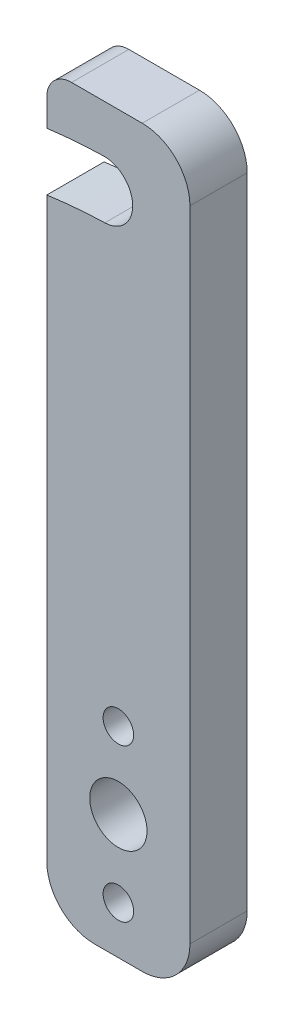
SolidWorks part; units mm, degrees
material "MDF"
ref_plane "Plano frontal" through (0, 0, 0) normal (0, 0, 1) x (1, 0, 0)
ref_plane "Plano superior" through (0, 0, 0) normal (0, 1, 0) x (1, 0, 0)
ref_plane "Plano direito" through (0, 0, 0) normal (1, 0, 0) x (0, 0, -1)
sketch "Esboço1" plane through (0, 0, 0) normal (0, 0, 1) x (1, 0, 0)
  line L0 (0, -17.4894) -> (0, -33.4894) construction
  line L1 (-7.5, -38.4894) -> (7.5, -38.4894)
  line L2 (-7.5, -38.4894) -> (-7.5, 38.4894)
  line L3 (-7.5, 38.4894) -> (7.5, 38.4894)
  line L4 (7.5, -38.4894) -> (7.5, 38.4894)
  line L5 (-7.5, -38.4894) -> (7.5, 38.4894) construction
  line L6 (-7.5, 38.4894) -> (7.5, -38.4894) construction
  circle A0 centre (0, -33.4894) radius 1.6
  circle A1 centre (0, -17.4894) radius 1.6
  arc A3 (-1.4989, 30.4905) -> (-7.9245, 29.947) centre (0, -25.4894) ccw construction
  arc A4 (-1.5792, 33.4894) -> (-8.3491, 32.9168) centre (0, -25.4894) ccw
  arc A5 (-1.4186, 27.4916) -> (-7.5, 26.9772) centre (0, -25.4894) ccw
  arc A6 (-1.4186, 27.4916) -> (-1.5792, 33.4894) centre (-1.4989, 30.4905) ccw
  arc A7 (-8.3491, 32.9168) -> (-7.5, 26.9772) centre (-7.9245, 29.947) ccw
  circle A8 centre (0, -25.4894) radius 3
  point P0 (0, 0)
  point P14 (-4.7196, 30.3113)
  point P20 (1.5, 30.5708)
  dimension "D1" = 56
  dimension "D2" = 3.2
  dimension "D4" = 16
  dimension "D6" = 3
  dimension "D8" = 6
  dimension "D3" = 15
  dimension "D5" = 5
  dimension "D7" = 5
  dimension "D9" = 6
extrude "Ressalto-extrusão1" add sketch "Esboço1" along normal blind 6
fillet "Filete1" radius 5 3 edges at (-7.5, -38.4894, 3) (7.5, -38.4894, 3) (7.5, 38.4894, 3)
fillet "Filete2" radius 2.6 1 edges at (-7.5, 38.4894, 3)
